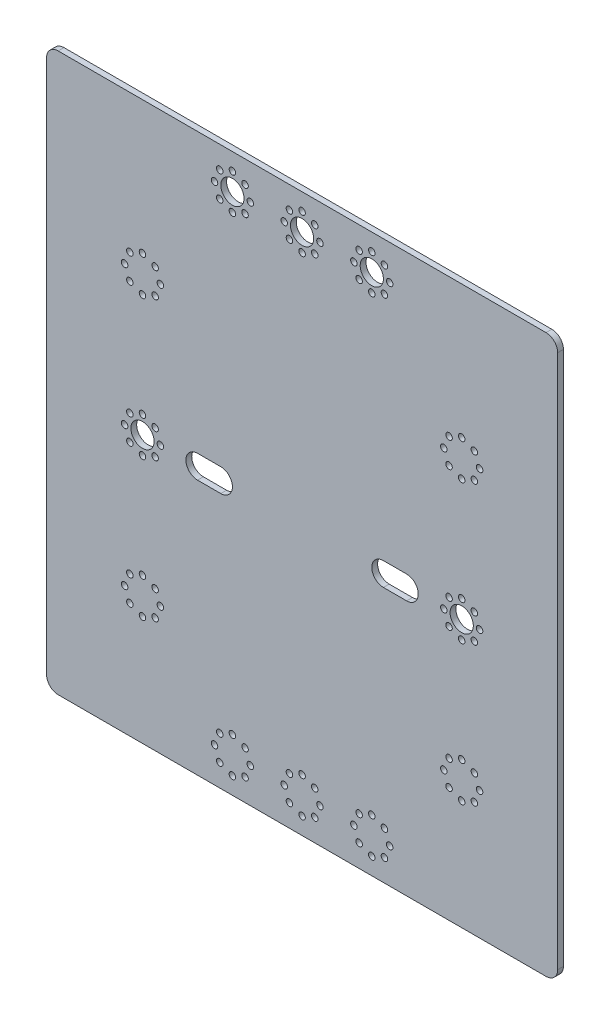
SolidWorks part; units mm, degrees
material "6061-T6 (SS)"
ref_plane "Front Plane" through (0, 0, 0) normal (0, 0, 1) x (1, 0, 0)
ref_plane "Top Plane" through (0, 0, 0) normal (0, 1, 0) x (1, 0, 0)
ref_plane "Right Plane" through (0, 0, 0) normal (1, 0, 0) x (0, 0, -1)
sketch "Sketch1" plane through (0, 0, 0) normal (0, 0, 1) x (1, 0, 0)
  line L1 (0, 0) -> (-279.4, 0)
  line L2 (0, 0) -> (0, -304.8)
  line L3 (0, -304.8) -> (-279.4, -304.8)
  line L4 (-279.4, 0) -> (-279.4, -304.8)
  dimension "D1" = 304.8
  dimension "D2" = 279.4
extrude "Boss-Extrude1" add sketch "Sketch1" along normal blind 3.175
sketch "Sketch2" plane through (0, 0, 3.175) normal (0, 0, 1) x (1, 0, 0)
  line L0 (-139.7, 0) -> (-139.7, -304.8) construction
  line L1 (0, 0) -> (-279.4, 0) construction
  line L2 (-279.4, -304.8) -> (0, -304.8) construction
  circle A0 centre (-139.7, -19.05) radius 6.35
  circle A2 centre (-226.949, -158.75) radius 6.35
  dimension "D1" = 12.7
  dimension "D6" = 12.7
  dimension "D2" = 19.05
  dimension "D5" = 139.7
  dimension "D8" = 87.249
extrude "Cut-Extrude1" cut sketch "Sketch2" against normal blind 3.175
sketch "Sketch3" plane through (0, 0, 3.175) normal (0, 0, 1) x (1, 0, 0)
  line L0 (-139.7, 0) -> (-139.7, -304.8) construction
  line L1 (0, 0) -> (-279.4, 0) construction
  line L2 (-279.4, -304.8) -> (0, -304.8) construction
  circle A0 centre (-139.7, -9.271) radius 1.778
  circle A1 centre (-139.7, -19.05) radius 6.35 construction
  dimension "D1" = 3.556
  dimension "D2" = 9.779
extrude "Cut-Extrude2" cut sketch "Sketch3" against normal blind 3.175
pattern_circular "CirPattern1" count 8 over 360 about axis through (-139.7, -19.05, 0) along (0, 0, 1) of "Cut-Extrude2"
sketch "Sketch4" plane through (0, 0, 3.175) normal (0, 0, 1) x (1, 0, 0)
  line L0 (-226.949, -158.75) -> (-226.949, 0) construction
  circle A0 centre (-226.949, -148.971) radius 1.778
  dimension "D1" = 3.556
  dimension "D2" = 9.779
extrude "Cut-Extrude3" cut sketch "Sketch4" against normal blind 3.175
pattern_circular "CirPattern2" count 8 over 360 about axis through (-226.949, -158.75, 0) along (0, 0, 1) of "Cut-Extrude3"
ref_plane "Plane1" through (-139.7, 0, 0) normal (-1, 0, 0) x (0, 0, 1)
mirror "Mirror1" about plane through (-139.7, 0, 0) normal (-1, 0, 0) of "Cut-Extrude1", "CirPattern2", "Cut-Extrude3"
pattern_linear "LPattern2" count 4 spacing 38.1 along (0, 1, 0) skipping (1, 0), (3, 0) of "Mirror1", "Cut-Extrude1", "Cut-Extrude3", "CirPattern2"
pattern_linear "LPattern3" count 4 spacing 38.1 along (0, -1, 0) skipping (1, 0), (3, 0) of "Cut-Extrude3", "CirPattern2"
sketch "Sketch5" plane through (0, 0, 3.175) normal (0, 0, 1) x (1, 0, 0)
  circle A0 centre (-226.949, -82.55) radius 6.35
  circle A1 centre (-52.451, -82.55) radius 6.35
extrude "Boss-Extrude4" add sketch "Sketch5" against normal blind 3.175
mirror "Mirror4" about plane through (-139.7, 0, 0) normal (-1, 0, 0) of "LPattern3"
sketch "Sketch6" plane through (0, 0, 3.175) normal (0, 0, 1) x (1, 0, 0)
  line L0 (-139.7, 1.7463) -> (-139.7, -1.7462) construction
  line L1 (0, 0) -> (-279.4, 0) construction
  circle A0 centre (-101.6, -19.05) radius 6.35
  circle A1 centre (-177.8, -19.05) radius 6.35
  dimension "D1" = 12.7
  dimension "D2" = 12.7
  dimension "D3" = 76.2
  dimension "D4" = 38.1
  dimension "D5" = 19.05
  dimension "D6" = 38.1
extrude "Cut-Extrude4" cut sketch "Sketch6" against normal blind 3.175 contours A1
sketch "Sketch7" plane through (0, 0, 3.175) normal (0, 0, 1) x (1, 0, 0)
  circle A0 centre (-177.8, -9.271) radius 1.778
  circle A1 centre (-177.8, -19.05) radius 6.35 construction
  dimension "D1" = 3.556
  dimension "D2" = 9.779
extrude "Cut-Extrude5" cut sketch "Sketch7" against normal blind 3.175
pattern_circular "CirPattern3" count 8 over 360 about axis through (-177.8, -19.05, 0) along (0, 0, 1) of "Cut-Extrude5"
sketch "Sketch8" plane through (0, 0, 3.175) normal (0, 0, 1) x (1, 0, 0)
  circle A0 centre (-101.6, -9.271) radius 1.778
  circle A1 centre (-101.6, -19.05) radius 6.35 construction
  dimension "D1" = 3.556
  dimension "D2" = 9.779
extrude "Cut-Extrude6" cut sketch "Sketch8" against normal blind 3.175
pattern_circular "CirPattern4" count 8 over 360 about axis through (-101.6, -19.05, 0) along (0, 0, 1) of "Cut-Extrude6"
ref_plane "Plane3" through (0, -152.4, 0) normal (0, 1, 0) x (1, 0, 0)
mirror "Mirror5" about plane through (0, -152.4, 0) normal (0, 1, 0) of "CirPattern3", "CirPattern4", "Cut-Extrude5", "Cut-Extrude6"
fillet "Fillet1" radius 6.35 4 edges at (0, 0, 1.5875) (-279.4, 0, 1.5875) (-279.4, -304.8, 1.5875) (0, -304.8, 1.5875)
sketch "Sketch10" plane through (0, 0, 3.175) normal (0, 0, 1) x (1, 0, 0)
  line L0 (-196.85, -158.75) -> (-184.15, -158.75) construction
  line L1 (-196.85, -152.4) -> (-184.15, -152.4)
  line L2 (-196.85, -165.1) -> (-184.15, -165.1)
  line L3 (1.7463, -152.4) -> (-1.7462, -152.4) construction
  line L4 (-139.7, 1.7463) -> (-139.7, -1.7462) construction
  arc A0 (-196.85, -152.4) -> (-196.85, -165.1) centre (-196.85, -158.75) ccw
  arc A1 (-184.15, -165.1) -> (-184.15, -152.4) centre (-184.15, -158.75) ccw
  point P2 (-190.5, -158.75)
  dimension "D1" = 12.7
  dimension "D2" = 12.7
  dimension "D3" = 6.35
  dimension "D4" = 50.8
extrude "Cut-Extrude8" cut sketch "Sketch10" against normal blind 3.175
mirror "Mirror7" about plane through (-139.7, 0, 0) normal (-1, 0, 0) of "Cut-Extrude8"
mirror "Mirror8" about plane through (0, -152.4, 0) normal (0, 1, 0) of "CirPattern1", "Cut-Extrude2"
